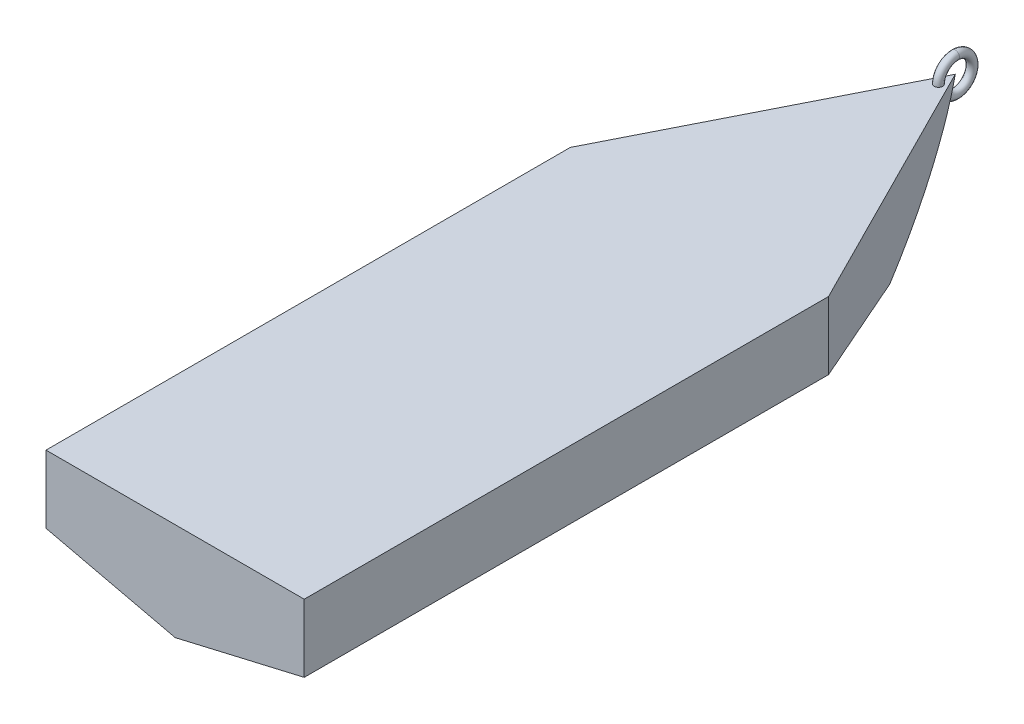
SolidWorks part; units mm, degrees
material "Rubber"
ref_plane "Front Plane" through (0, 0, 0) normal (0, 0, 1) x (1, 0, 0)
ref_plane "Top Plane" through (0, 0, 0) normal (0, 1, 0) x (1, 0, 0)
ref_plane "Right Plane" through (0, 0, 0) normal (1, 0, 0) x (0, 0, -1)
sketch "Cross-Section B Sketch" plane through (0, 0, 0) normal (0, 0, 1) x (1, 0, 0)
  line L5 (-0.0006, -30.4064) -> (37.5282, -12.9064)
  line L6 (37.5282, -12.9064) -> (37.5282, 26.4536)
  line L7 (37.5282, 26.4536) -> (-37.5294, 26.4536)
  line L8 (-37.5294, -12.9064) -> (-37.5294, 26.4536)
  line L9 (-0.0006, -30.4064) -> (-37.5294, -12.9064)
  line L10 (-76.707, -30.4064) -> (84.3947, -30.4064) construction
  dimension "Deadrise Angle" = 25
  dimension "Width" = 75.0576
  dimension "Height" = 56.86
sketch "Fore-Aft" plane through (0, 0, 0) normal (1, 0, 0) x (0, 0, -1)
  line L0 (0, 0) -> (62.0342, 0) construction
  line L1 (76.2, 28.4649) -> (-76.2, 28.4649)
  line L2 (151.4715, 28.4649) -> (76.2, 28.4649)
  line L4 (76.2, -30.4064) -> (-76.2, -30.4064)
  line L6 (-76.2, 28.4649) -> (-76.2, -30.4064)
  line L7 (76.2, -30.4064) -> (76.2, 28.4649)
  point P6 (0, 28.4649)
  point P9 (0, -30.4064)
  dimension "D1" = 152.4
  dimension "D2" = 58.8713
ref_plane "Cross-Section A Plane " through (0, 0, -76.2) normal (0, 0, -1) x (-1, 0, 0)
sketch "Cross-Section A Sketch" plane through (0, 0, -76.2) normal (0, 0, -1) x (-1, 0, 0)
  line L5 (-0.0006, -30.4064) -> (37.5282, -12.9064)
  line L6 (37.5282, -12.9064) -> (37.5282, 26.4536)
  line L7 (37.5282, 26.4536) -> (-37.5294, 26.4536)
  line L8 (-37.5294, -12.9064) -> (-37.5294, 26.4536)
  line L9 (-0.0006, -30.4064) -> (-37.5294, -12.9064)
  line L10 (-76.707, -30.4064) -> (84.3947, -30.4064) construction
  dimension "Deadrise Angle" = 25
  dimension "Width" = 75.0576
  dimension "Height" = 56.86
ref_plane "Cross-Section C Plane" through (0, 0, 76.2) normal (0, 0, -1) x (-1, 0, 0)
sketch "Cross-Section C Sketch" plane through (0, 0, 76.2) normal (0, 0, 1) x (1, 0, 0)
  line L5 (-0.0006, -30.4064) -> (37.5282, -12.9064)
  line L6 (37.5282, -12.9064) -> (37.5282, 26.4536)
  line L7 (37.5282, 26.4536) -> (-37.5294, 26.4536)
  line L8 (-37.5294, -12.9064) -> (-37.5294, 26.4536)
  line L9 (-0.0006, -30.4064) -> (-37.5294, -12.9064)
  line L10 (-76.707, -30.4064) -> (84.3947, -30.4064) construction
  dimension "Deadrise Angle" = 25
  dimension "Width" = 75.0576
  dimension "Height" = 56.86
loft "Fore-Aft Loft" add profiles "Cross-Section C Sketch", "Cross-Section B Sketch", "Cross-Section A Sketch"
sketch "Port-Starboard Profile" plane through (0, 0, 0) normal (1, 0, 0) x (0, 0, -1)
  line L4 (76.2, 26.4536) -> (-76.2, 26.4536) construction
  line L5 (76.2, 26.4536) -> (-76.2, 26.4536) construction
  line L7 (150.5603, 26.4536) -> (150.5603, -30.4064)
  line L8 (76.2, -30.4064) -> (150.5603, -30.4064)
  arc A1 (76.2, -30.4064) -> (150.5603, 26.4536) centre (75.8165, 47.1485) ccw
  dimension "Bow Curve Radius" = 77.5558
  dimension "Bow Length" = 74.3603
sketch "Top Bow Profile" plane through (0, 26.4536, 0) normal (0, 1, 0) x (1, 0, 0)
  line L0 (37.5294, 76.2) -> (0, 150.5603)
  line L1 (0, 76.2) -> (0, 150.5603) construction
  line L3 (-37.5282, 76.2) -> (37.5294, 76.2)
  line L4 (0, 150.5603) -> (-37.5282, 76.2)
extrude "Top Bow Extrusion" add sketch "Top Bow Profile" against normal up to vertex (56.86 mm away) up to point (0, -30.4064, -150.5603)
extrude "Port-Starboard Cut" cut sketch "Port-Starboard Profile" against normal through all both and the other way through all contours A1 L8 L7
sketch "Fore-Aft Bow Construction Sketch" plane through (0, 0, -76.2) normal (0, 0, 1) x (1, 0, 0)
  line L0 (37.5294, -30.4064) -> (37.5294, -12.9064) construction
  line L1 (37.5294, -12.9064) -> (0.0006, -30.4064) construction
  line L2 (0.0006, -30.4064) -> (37.5294, -30.4064) construction
  line L3 (-37.5282, -30.4064) -> (0.0006, -30.4064) construction
  line L4 (0.0006, -30.4064) -> (-37.5282, -12.9064) construction
  line L5 (-37.5282, -12.9064) -> (-37.5282, -30.4064) construction
  line L6 (37.5294, -30.4064) -> (37.5294, -12.9064)
  line L7 (37.5294, -12.9064) -> (0.0006, -30.4064)
  line L8 (0.0006, -30.4064) -> (37.5294, -30.4064)
  line L9 (-37.5282, -30.4064) -> (0.0006, -30.4064)
  line L10 (0.0006, -30.4064) -> (-37.5282, -12.9064)
  line L11 (-37.5282, -12.9064) -> (-37.5282, -30.4064)
extrude "Fore-aft bow wrapup extrustion" cut sketch "Fore-Aft Bow Construction Sketch" against normal up to next contours L7 L8 L6
scale "Scale" scale about centroid uniform scaling no x scale factor 2 y scale factor 2 z scale factor 2
shell "Shell2" thickness 2.54
scale "Scale1" scale about centroid uniform scaling no x scale factor 0.65 y scale factor 0.325 z scale factor 0.65
sketch "Sketch1" plane through (0, 0, 0) normal (1, 0, 0) x (0, 0, -1)
  circle A0 centre (190.4999, 19.2587) radius 6.35
ref_plane "Plane1" through (0, 0, -190.4999) normal (0, 0, 1) x (1, 0, 0)
sketch "Sketch2" plane through (0, 0, -190.4999) normal (0, 0, 1) x (1, 0, 0)
  line L0 (0, 12.9087) -> (0, 25.6087) construction
  circle A0 centre (0, 25.6087) radius 1.5875
sweep "Sweep1" add profiles "Sketch2" path "Sketch1"
